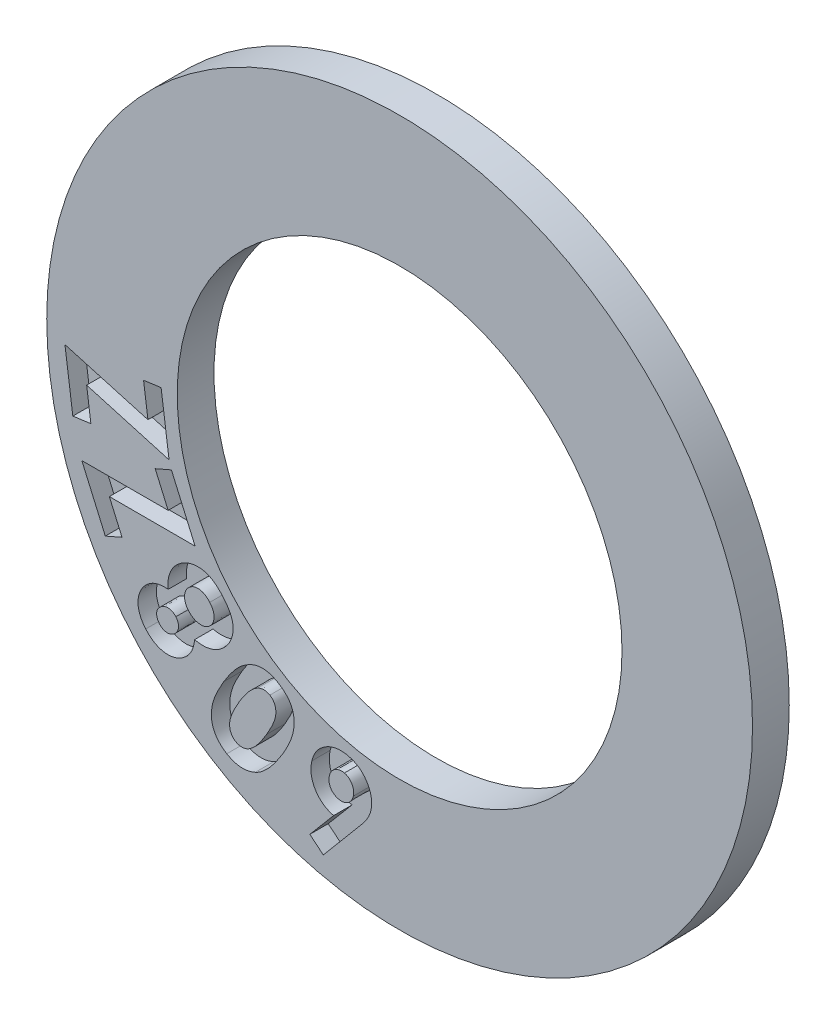
SolidWorks part; units mm, degrees
ref_plane "Front Plane" through (0, 0, 0) normal (0, 0, 1) x (1, 0, 0)
ref_plane "Top Plane" through (0, 0, 0) normal (0, 1, 0) x (1, 0, 0)
ref_plane "Right Plane" through (0, 0, 0) normal (1, 0, 0) x (0, 0, -1)
sketch "Sketch1" plane through (0, 0, 0) normal (0, 0, 1) x (1, 0, 0)
  circle A0 centre (0, 0) radius 6.05
  circle A1 centre (0, 0) radius 9.6
  circle A2 centre (0, 0) radius 6.4983 construction
  dimension "Bearing Sheild Inner" = 12.1
  dimension "Bearing Sheild Outter" = 19.2
extrude "Boss-Extrude1" add sketch "Sketch1" along normal blind 1 contours A1 A0
sketch "Sketch2" plane through (0, 0, 1) normal (0, 0, -1) x (-1, 0, 0)
  text T0 "<b>608ZZ</b>" font "Century Gothic" height in points 10
extrude "Cut-Extrude1" cut sketch "Sketch2" along normal blind 0.5
equation "\"Motor Width\"= 42.3'eg: For stepper motor Nema 17 = 42.3mm"
equation "\"Motor Hole Config Width\"= 31'eg: For stepper motor Nema 17 = 31"
equation "\"Mounting Hole Diameter\"= 3'eg: For Nema 17 3mm"
equation "\"Motor Depth\"= 50'eg: For Nema 17 50mm"
equation "\"Exposed Shaft Length\"= 22'eg: For Nema 17 22mm"
equation "\"Shaft Seround Depthr\"= 2'eg: For Nema 17 2mm"
equation "\"Shaft Diameter\"= 5'eg: For Nema 17 5mm"
equation "\"Top/Bottom Casing Depth\"= 10'Guess"
equation "\"Mid Casing Depth\"= \"Motor Depth\" - 2 * ( \"Top/Bottom Casing Depth\" )"
equation "\"Bearing Outter Diameter\"= 22' From Spec 608z = 22mm"
equation "\"Shaft Clearance Hole\"= \"Shaft Diameter\"+1.5'Guess"
equation "\"Bearing Ball Size\"= 3.969'From Spec"
equation "\"Bearing Inner Case Inner Diameter\"= 8'From Spec"
equation "\"Bearing Inner Case Outter Diameter\"= 12.1'From Spec"
equation "\"Bearing Outter Case Inner Diameter\"= 19.2'From Spec"
equation "\"Bearing Width\"= 7'From Spec"
equation "\"Bearing Sheild Outter@Sketch1\"=\"Bearing Outter Case Inner Diameter\""
equation "\"Bearing Sheild Inner@Sketch1\"=\"Bearing Inner Case Outter Diameter\""
